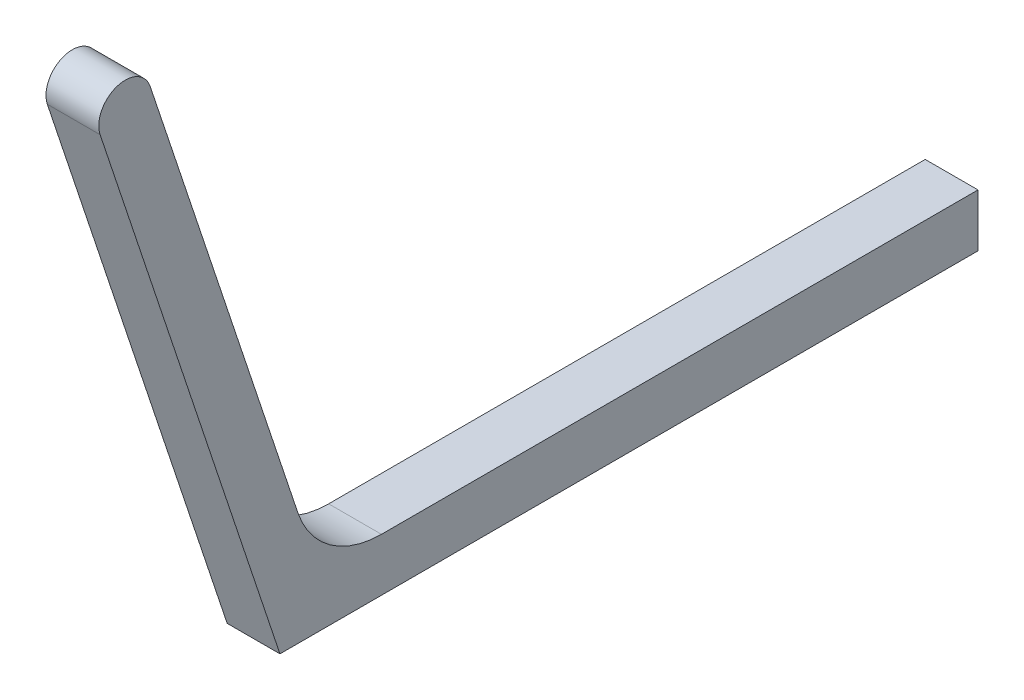
SolidWorks part; units mm, degrees
material "ABS"
ref_plane "Alzado" through (0, 0, 0) normal (0, 0, 1) x (1, 0, 0)
ref_plane "Planta" through (0, 0, 0) normal (0, 1, 0) x (1, 0, 0)
ref_plane "Vista lateral" through (0, 0, 0) normal (1, 0, 0) x (0, 0, -1)
ref_plane "Plano1" through (3, 0, 0) normal (1, 0, 0) x (0, 0, -1)
sketch "Croquis1" plane through (3, 0, 0) normal (1, 0, 0) x (0, 0, -1)
  line L0 (-143.3676, 342.7136) -> (-122.931, 281.4037)
  line L1 (-122.931, 281.4037) -> (-43.6064, 281.4037)
  line L2 (-43.6064, 281.4037) -> (-43.6064, 287.4037)
  line L3 (-43.6064, 287.4037) -> (-111.3988, 287.4037)
  line L4 (-120.8857, 294.2415) -> (-137.6755, 344.6109)
  arc A0 (-137.6755, 344.6109) -> (-143.3676, 342.7136) centre (-140.5216, 343.6623) ccw
  arc A1 (-111.3988, 287.4037) -> (-120.8857, 294.2415) centre (-111.3988, 297.4037) cw
extrude "Saliente-Extruir1" add sketch "Croquis1" against normal blind 6
